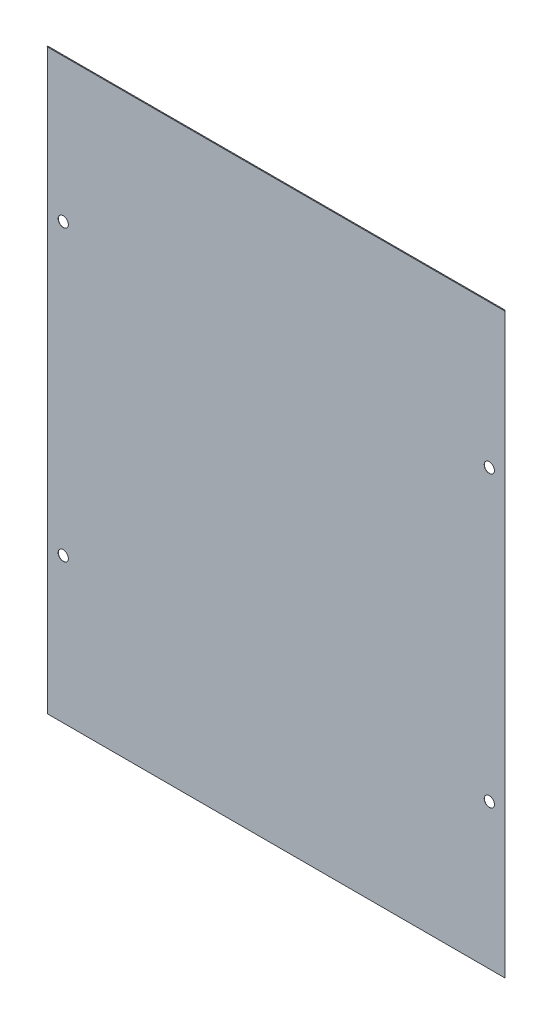
SolidWorks part; units mm, degrees
material "Kapton Film"
ref_plane "Front Plane" through (0, 0, 0) normal (0, 0, 1) x (1, 0, 0)
ref_plane "Top Plane" through (0, 0, 0) normal (0, 1, 0) x (1, 0, 0)
ref_plane "Right Plane" through (0, 0, 0) normal (1, 0, 0) x (0, 0, -1)
sketch "Sketch1" plane through (0, 0, 0) normal (0, 0, 1) x (1, 0, 0)
  line L0 (0, 113.6448) -> (0, -113.6448)
  line L1 (-89.8724, -113.6448) -> (89.8724, -113.6448)
  line L2 (-89.8724, -113.6448) -> (-89.8724, 113.6448)
  line L3 (-89.8724, 113.6448) -> (89.8724, 113.6448)
  line L4 (89.8724, -113.6448) -> (89.8724, 113.6448) construction
  line L5 (-83.72, 56.9862) -> (-83.72, -56.6662) construction
  circle A0 centre (-83.72, 56.9862) radius 2
  circle A1 centre (-83.72, -56.6662) radius 2
  dimension "D3" = 4
  dimension "D4" = 4
  dimension "D1" = 179.7448
  dimension "D2" = 227.2896
  dimension "D5" = 6.1524
  dimension "D6" = 113.6524
  dimension "D7" = 56.6586
extrude "Body" add sketch "Sketch1" along normal blind 0.0686 contours L3 L2 L1 L0 A1 A0
sketch "Sketch2" plane through (0, 227.3734, 0.0686) normal (0, 0, 1) x (-1, 0, 0)
  line L1 (89.8724, 113.7286) -> (0, 113.7286)
  line L2 (89.8724, 113.7286) -> (89.8724, 113.7972)
  line L3 (89.8724, 113.7972) -> (0, 113.7972)
  line L4 (0, 113.7286) -> (0, 113.7972)
  dimension "D1" = 0.0686
extrude "Top Overwrap" add sketch "Sketch2" along normal blind 0.2896
mirror "Mirror1" about plane through (0, 0, 0) normal (1, 0, 0) of "Top Overwrap", "Body"
